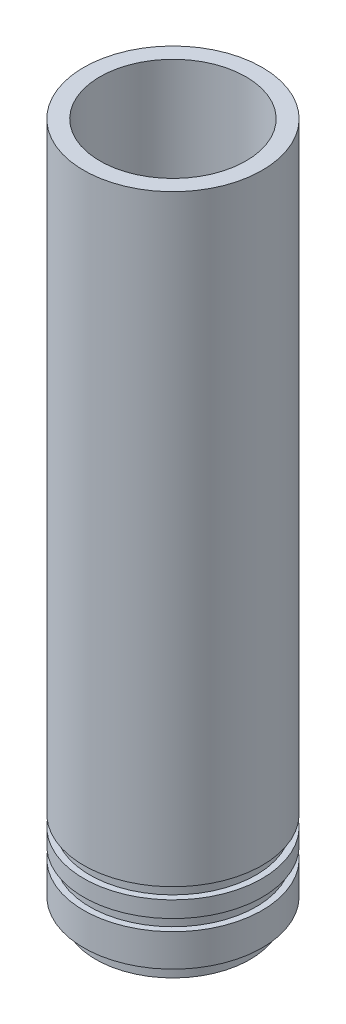
SolidWorks part; units mm, degrees
material "A-Glass Fiber"
ref_plane "Front Plane" through (0, 0, 0) normal (0, 0, 1) x (1, 0, 0)
ref_plane "Top Plane" through (0, 0, 0) normal (0, 1, 0) x (1, 0, 0)
ref_plane "Right Plane" through (0, 0, 0) normal (1, 0, 0) x (0, 0, -1)
sketch "Sketch1" plane through (0, 0, 0) normal (0, 0, 1) x (1, 0, 0)
  line L0 (0, 0) -> (0, 60.7939) construction
  line L1 (16, 0) -> (9.5, 24.2583)
  line L2 (9.5, 24.2583) -> (9.5, 29.2583)
  line L3 (9.5, 29.2583) -> (18, 37.7583)
  line L4 (18, 37.7583) -> (18, 170)
  line L5 (18, 170) -> (22, 170)
  line L6 (22, 170) -> (22, 21.6)
  line L7 (22, 21.6) -> (20.5, 21.6)
  line L8 (20.5, 21.6) -> (20.5, 18.8)
  line L9 (20.5, 18.8) -> (22, 18.8)
  line L10 (22, 18.8) -> (22, 14.8)
  line L11 (22, 14.8) -> (20.5, 14.8)
  line L12 (20.5, 14.8) -> (20.5, 12)
  line L13 (20.5, 12) -> (22, 12)
  line L14 (22, 12) -> (22, 4)
  line L15 (22, 4) -> (19, 4)
  line L16 (19, 4) -> (19, 0)
  line L17 (19, 0) -> (16, 0)
  dimension "D1" = 44
  dimension "D2" = 36
  dimension "D3" = 19
  dimension "D4" = 32
  dimension "D5" = 4
  dimension "D6" = 170
  dimension "D7" = 1.5
  dimension "D8" = 2.8
  dimension "D9" = 4
  dimension "D10" = 8
  dimension "D11" = 38
  dimension "D12" = 5
  dimension "D13" = 15
  dimension "D14" = 45
revolve "Revolve1" add sketch "Sketch1" angle 360 about L0
fillet "Fillet1" radius 5 2 edges at (0, 29.2583, -9.5) (0, 24.2583, -9.5)
